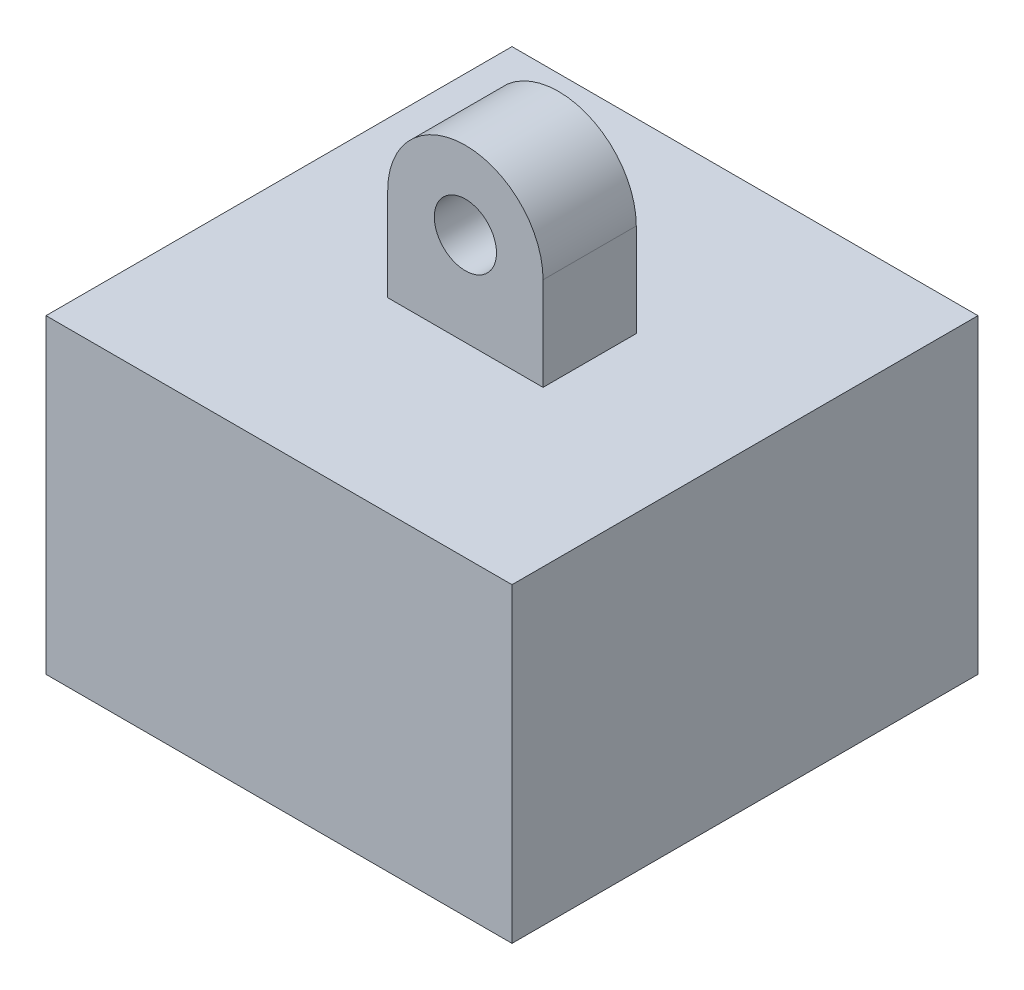
SolidWorks part; units mm, degrees
ref_plane "Front Plane" through (0, 0, 0) normal (0, 0, 1) x (1, 0, 0)
ref_plane "Top Plane" through (0, 0, 0) normal (0, 1, 0) x (1, 0, 0)
ref_plane "Right Plane" through (0, 0, 0) normal (1, 0, 0) x (0, 0, -1)
sketch "Sketch1" plane through (0, 0, 0) normal (0, -1, 0) x (1, 0, 0)
  line L1 (0, 0) -> (15, 0)
  line L2 (0, 0) -> (0, -15)
  line L3 (0, -15) -> (15, -15)
  line L4 (15, 0) -> (15, -15)
  dimension "D1" = 15
  dimension "D2" = 15
extrude "Boss-Extrude1" add sketch "Sketch1" along normal blind 10
ref_plane "Plane2" through (0, 0, -7.5) normal (0, 0, 1) x (1, 0, 0)
sketch "Sketch4" plane through (0, 0, -7.5) normal (0, 0, 1) x (1, 0, 0)
  line L0 (15, 0) -> (0, 0) construction
  line L1 (5, 3) -> (10, 3)
  line L2 (5, 3) -> (5, 0)
  line L3 (5, 0) -> (10, 0)
  line L4 (10, 3) -> (10, 0)
  line L5 (5, 3) -> (10, 0) construction
  line L6 (5, 0) -> (10, 3) construction
  arc A1 (10, 3) -> (5, 3) centre (7.5, 3) ccw
  circle A2 centre (7.5, 3) radius 1
  point P0 (7.5, 1.5)
  point P5 (7.5, 0)
  point P8 (7.5, 0)
  dimension "D3" = 2
  dimension "D1" = 3
  dimension "D2" = 5
extrude "Boss-Extrude2" add sketch "Sketch4" along normal mid plane 3 contours A2 L1 L2 L3 L4 | A2 L1 A1
